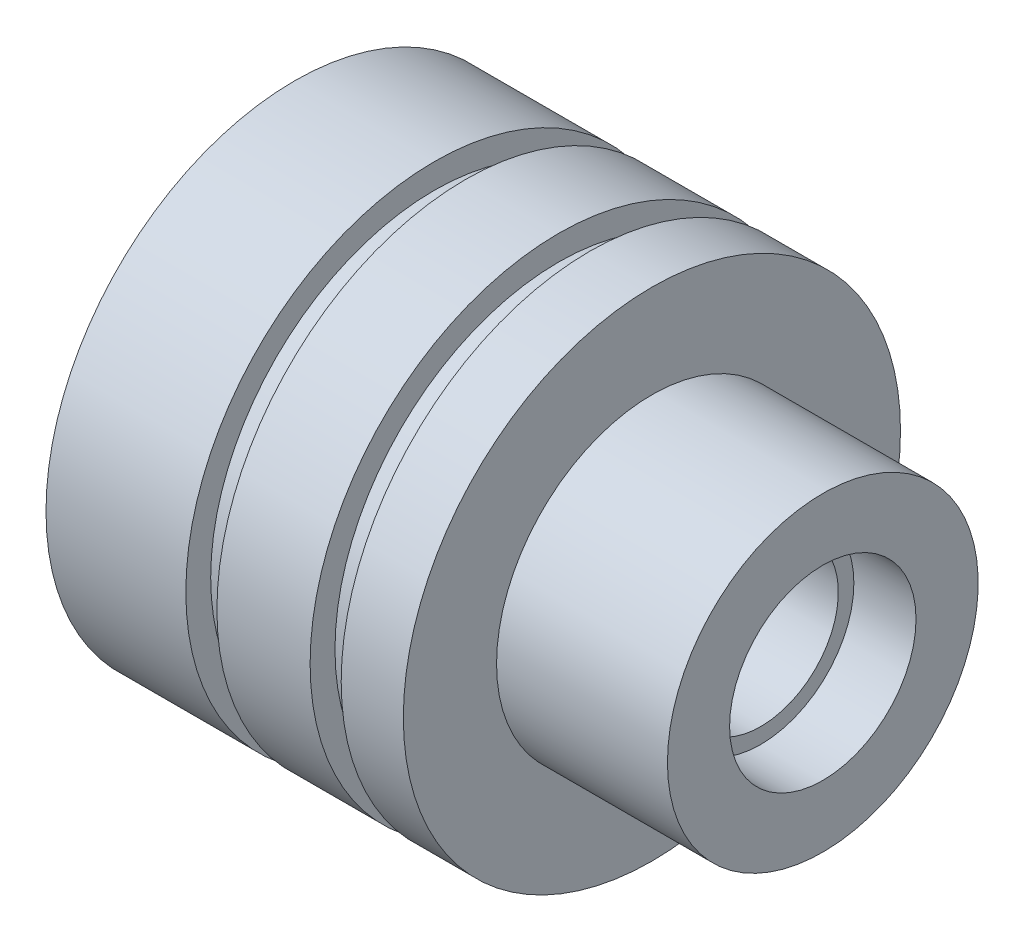
SolidWorks part; units mm, degrees
ref_plane "Ebene vorne" through (0, 0, 0) normal (0, 0, 1) x (1, 0, 0)
ref_plane "Ebene oben" through (0, 0, 0) normal (0, 1, 0) x (1, 0, 0)
ref_plane "Ebene rechts" through (0, 0, 0) normal (1, 0, 0) x (0, 0, -1)
sketch "Skizze1" plane through (0, 0, 0) normal (0, 0, 1) x (1, 0, 0)
  line L0 (0, 0) -> (17, 0) construction
  line L1 (0, 8) -> (0, 5)
  line L2 (0, 8) -> (4.5, 8)
  line L3 (4.5, 8) -> (4.5, 7.2)
  line L4 (4.5, 7.2) -> (5.5, 7.2)
  line L5 (5.5, 7.2) -> (5.5, 8)
  line L6 (5.5, 8) -> (8.5, 8)
  line L7 (8.5, 8) -> (8.5, 7.2)
  line L8 (8.5, 7.2) -> (9.5, 7.2)
  line L9 (9.5, 7.2) -> (9.5, 8)
  line L10 (9.5, 8) -> (11.5, 8)
  line L12 (15, 2.5) -> (15, 3)
  line L13 (15, 3) -> (17, 3)
  line L14 (17, 3) -> (17, 5)
  line L15 (17, 5) -> (11.5, 5)
  line L16 (11.5, 5) -> (11.5, 8)
  line L17 (0, 0) -> (0, 5) construction
  line L18 (17, 0) -> (17, 3) construction
  line L19 (0, 5) -> (5.6, 5)
  line L20 (5.6, 5) -> (5.6, 2.5)
  line L21 (5.6, 2.5) -> (15, 2.5)
  dimension "D1" = 17
  dimension "D2" = 10
  dimension "D3" = 2
  dimension "D4" = 16
  dimension "D5" = 10
  dimension "D6" = 6
  dimension "D7" = 5.5
  dimension "D8" = 0.8
  dimension "D9" = 1
  dimension "D10" = 2
  dimension "D11" = 6
  dimension "D12" = 1
  dimension "D13" = 5
  dimension "D14" = 9.4
revolve "Rotation1" add sketch "Skizze1" angle 360 about L0
